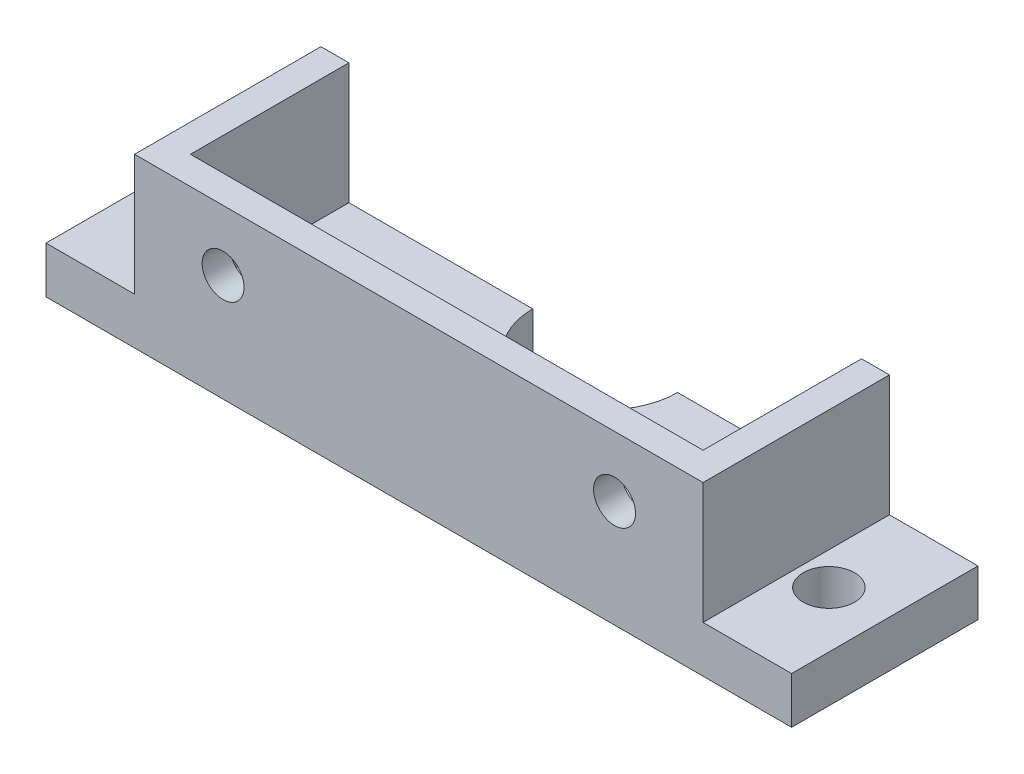
SolidWorks part; units mm, degrees
ref_plane "Front Plane" through (0, 0, 0) normal (0, 0, 1) x (1, 0, 0)
ref_plane "Top Plane" through (0, 0, 0) normal (0, 1, 0) x (1, 0, 0)
ref_plane "Right Plane" through (0, 0, 0) normal (1, 0, 0) x (0, 0, -1)
sketch "Sketch1" plane through (0, 0, 0) normal (0, 1, 0) x (1, 0, 0)
  line L1 (-40, 10) -> (40, 10)
  line L2 (-40, 10) -> (-40, -10)
  line L3 (-40, -10) -> (40, -10)
  line L4 (40, 10) -> (40, -10)
  line L5 (-40, 10) -> (40, -10) construction
  line L6 (-40, -10) -> (40, 10) construction
  point P0 (0, 0)
  dimension "D1" = 80
  dimension "D2" = 20
extrude "Boss-Extrude1" add sketch "Sketch1" along normal blind 5
sketch "Sketch2" plane through (0, 5, 0) normal (0, 1, 0) x (1, 0, 0)
  circle A0 centre (-34, 0) radius 2.75
  circle A1 centre (34, 0) radius 2.75
  dimension "D1" = 5.5
  dimension "D2" = 5.5
  dimension "D3" = 68
  dimension "D4" = 34
extrude "Cut-Extrude1" cut sketch "Sketch2" against normal blind 5
sketch "Sketch3" plane through (0, 0, 10) normal (0, 0, 1) x (1, 0, 0)
  line L0 (-40, 5) -> (40, 5) construction
  line L1 (-40, 5) -> (-40, 0) construction
  line L2 (-30.5, 18) -> (30.5, 18)
  line L3 (-30.5, 18) -> (-30.5, 5)
  line L4 (-30.5, 5) -> (30.5, 5)
  line L5 (30.5, 18) -> (30.5, 5)
  line L6 (-30.5, 18) -> (30.5, 5) construction
  line L7 (-30.5, 5) -> (30.5, 18) construction
  circle A0 centre (-21, 11.5) radius 2.25
  circle A1 centre (21, 11.5) radius 2.25
  point P7 (0, 11.5)
  dimension "D7" = 4.5
  dimension "D8" = 4.5
  dimension "D1" = 21
  dimension "D2" = 42
  dimension "D3" = 6.5
  dimension "D4" = 61
  dimension "D5" = 30.5
  dimension "D6" = 9.5
extrude "Boss-Extrude2" add sketch "Sketch3" against normal blind 3
sketch "Sketch4" plane through (0, 0, 7) normal (0, 0, -1) x (-1, 0, 0)
  line L0 (30.5, 5) -> (-30.5, 5) construction
  line L1 (-30.5, 18) -> (-27.5, 18)
  line L2 (-30.5, 18) -> (-30.5, 5)
  line L3 (-30.5, 5) -> (-27.5, 5)
  line L4 (-27.5, 18) -> (-27.5, 5)
  line L5 (-40, 5) -> (40, 5) construction
  line L6 (30.5, 18) -> (27.5, 18)
  line L7 (30.5, 18) -> (30.5, 5)
  line L8 (30.5, 5) -> (27.5, 5)
  line L9 (27.5, 18) -> (27.5, 5)
  dimension "D1" = 3
  dimension "D2" = 3
extrude "Boss-Extrude3" add sketch "Sketch4" along normal blind 17
sketch "Sketch5" plane through (0, 5, 0) normal (0, 1, 0) x (1, 0, 0)
  line L0 (27.5, 10) -> (-27.5, 10) construction
  circle A0 centre (0, 10) radius 7.7713
extrude "Cut-Extrude2" cut sketch "Sketch5" against normal blind 17
